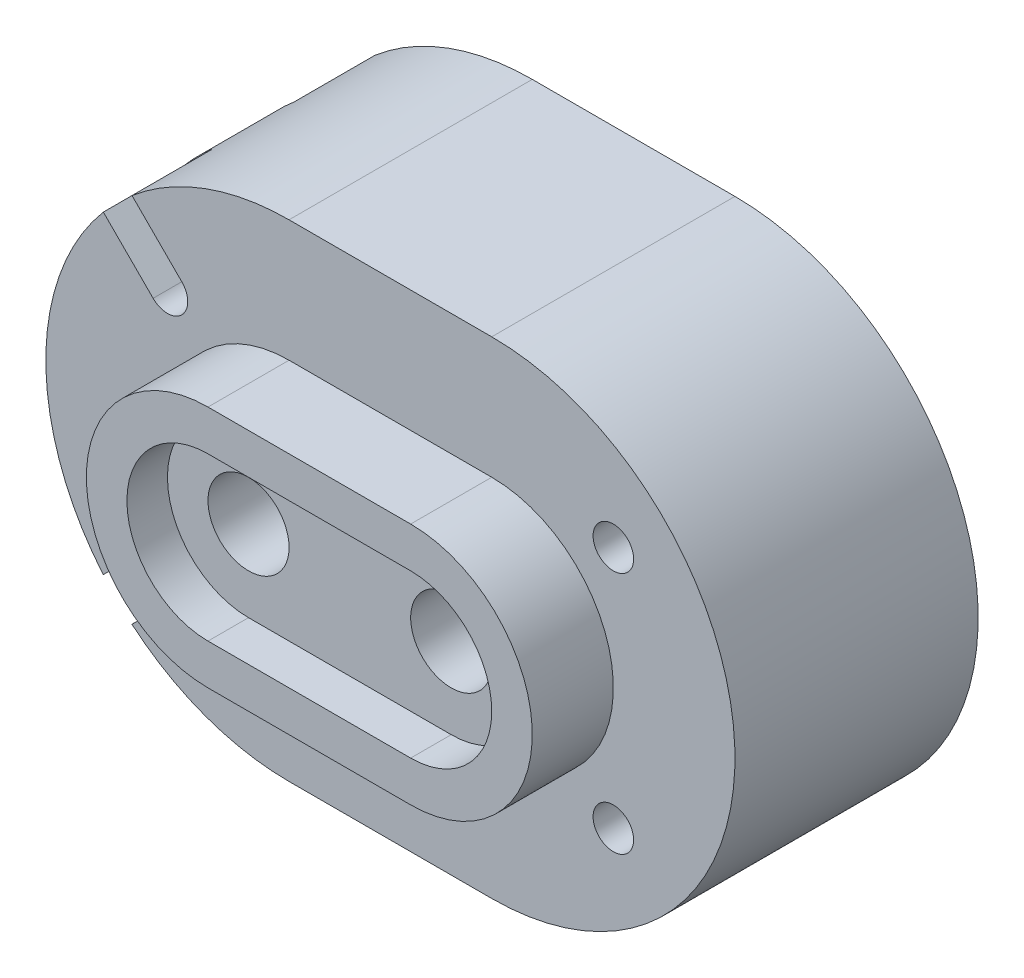
SolidWorks part; units mm, degrees
ref_plane "Front Plane" through (0, 0, 0) normal (0, 0, 1) x (1, 0, 0)
ref_plane "Top Plane" through (0, 0, 0) normal (0, 1, 0) x (1, 0, 0)
ref_plane "Right Plane" through (0, 0, 0) normal (1, 0, 0) x (0, 0, -1)
sketch "Sketch1" plane through (0, 0, 0) normal (0, 0, 1) x (1, 0, 0)
  line L0 (0, 0) -> (-25, 0)
  line L1 (-25, 60) -> (0, 60)
  arc A0 (-25, 0) -> (-25, 60) centre (-25, 30) cw
  arc A1 (0, 60) -> (0, 0) centre (0, 30) cw
  dimension "D2" = 25
  dimension "D1" = 30
extrude "Boss-Extrude3" add sketch "Sketch1" along normal blind 30
sketch "Sketch3" plane through (0, 0, 30) normal (0, 0, 1) x (1, 0, 0)
  line L0 (-25, 0) -> (0, 0) construction
  line L3 (-25, 30) -> (0, 30) construction
  line L4 (-25, 45) -> (0, 45)
  line L5 (-25, 15) -> (0, 15)
  arc A0 (-25, 60) -> (-25, 0) centre (-25, 30) ccw construction
  arc A2 (-25, 45) -> (-25, 15) centre (-25, 30) ccw
  arc A3 (0, 15) -> (0, 45) centre (0, 30) ccw
  point P2 (-55, 30)
  point P7 (-12.5, 30)
  dimension "D2" = 15
  dimension "D3" = 30
  dimension "D4" = 30
  dimension "D1" = 25
extrude "Boss-Extrude4" add sketch "Sketch3" along normal blind 10
sketch "Sketch4" plane through (0, 0, 40) normal (0, 0, 1) x (1, 0, 0)
  line L0 (-25, 30) -> (0, 30) construction
  line L1 (-25, 40) -> (0, 40)
  line L2 (-25, 20) -> (0, 20)
  arc A0 (-25, 40) -> (-25, 20) centre (-25, 30) ccw
  arc A1 (0, 20) -> (0, 40) centre (0, 30) ccw
  point P3 (-12.5, 30)
  dimension "D1" = 10
  dimension "D2" = 25
extrude "Cut-Extrude1" cut sketch "Sketch4" against normal blind 5
sketch "Sketch5" plane through (0, 0, 35) normal (0, 0, 1) x (1, 0, 0)
  circle A0 centre (-25, 30) radius 5
  circle A1 centre (0, 30) radius 5
  dimension "D1" = 10
  dimension "D2" = 10
  dimension "D3" = 25
  dimension "D4" = 10
extrude "Cut-Extrude2" cut sketch "Sketch5" against normal blind 122
sketch "Sketch6" plane through (0, 0, 30) normal (0, 0, 1) x (1, 0, 0)
  circle A0 centre (15, 45) radius 2.5
  circle A1 centre (15, 15) radius 2.5
  dimension "D1" = 5
  dimension "D4" = 5
  dimension "D2" = 15
  dimension "D3" = 15
  dimension "D5" = 15
extrude "Cut-Extrude4" cut sketch "Sketch6" against normal blind 10
sketch "Sketch7" plane through (0, 0, 30) normal (0, 0, 1) x (1, 0, 0)
  line L0 (-38.2322, 46.7678) -> (-44.3717, 52.9072)
  line L1 (-41.7678, 43.2322) -> (-47.9072, 49.3717)
  line L2 (-44.3809, 7.1006) -> (-38.2347, 13.2298)
  line L3 (-47.915, 10.6376) -> (-41.7688, 16.7667)
  circle A0 centre (-40, 45) radius 2.5
  circle A2 centre (-40, 15) radius 2.5
  arc A4 (-25, 60) -> (-25, 0) centre (-25, 30) ccw construction
  point P19 (-38.2347, 13.2298)
  point P20 (-41.7688, 16.7667)
  dimension "D1" = 5
  dimension "D5" = 5
  dimension "D2" = 40
  dimension "D3" = 15
  dimension "D4" = 30
  dimension "D6" = 8.68
extrude "Cut-Extrude9" cut sketch "Sketch7" against normal blind 10 contours A2 L3 A0 L2 | A2 | A0 | A0 L0 L1
sketch "Sketch9" plane through (0, 0, 20) normal (0, 0, 1) x (1, 0, 0)
  circle A0 centre (-40, 45) radius 2.5
  circle A1 centre (-40, 15) radius 2.5
  dimension "D1" = 5
  dimension "D2" = 5
extrude "Boss-Extrude5" add sketch "Sketch9" along normal blind 1.5
ref_plane "Plane1" through (0, 0, 15) normal (0, 0, 1) x (1, 0, 0)
mirror "Mirror1" about plane through (0, 0, 15) normal (0, 0, 1) of "Cut-Extrude9"
sketch "Sketch10" plane through (0, 0, 21.5) normal (0, 0, 1) x (1, 0, 0)
  arc A2 (-38.2322, 46.7678) -> (-41.7678, 43.2322) centre (-40, 45) ccw
  arc A3 (-41.7678, 43.2322) -> (-38.2322, 46.7678) centre (-40, 45) ccw
  arc A4 (-38.2322, 46.7678) -> (-41.7678, 43.2322) centre (-40, 45) ccw
  arc A5 (-41.7678, 43.2322) -> (-38.2322, 46.7678) centre (-40, 45) ccw
  arc A6 (-41.7688, 16.7667) -> (-38.2347, 13.2298) centre (-40, 15) ccw
  arc A7 (-38.2347, 13.2298) -> (-41.7688, 16.7667) centre (-40, 15) ccw
  arc A8 (-41.7688, 16.7667) -> (-38.2347, 13.2298) centre (-40, 15) ccw
  arc A9 (-38.2347, 13.2298) -> (-41.7688, 16.7667) centre (-40, 15) ccw
  dimension "D1" = 0
  dimension "D2" = 0
extrude "Cut-Extrude10" cut sketch "Sketch10" against normal blind 30
sketch "Sketch11" plane through (0, 0, 0) normal (0, 0, -1) x (-1, 0, 0)
  line L0 (0, 30) -> (25, 30) construction
  line L1 (0, 40) -> (25, 40)
  line L2 (0, 20) -> (25, 20)
  arc A0 (0, 40) -> (0, 20) centre (0, 30) ccw
  arc A1 (25, 20) -> (25, 40) centre (25, 30) ccw
  point P4 (12.5, 30)
  dimension "D1" = 10
extrude "Cut-Extrude11" cut sketch "Sketch11" against normal blind 15
